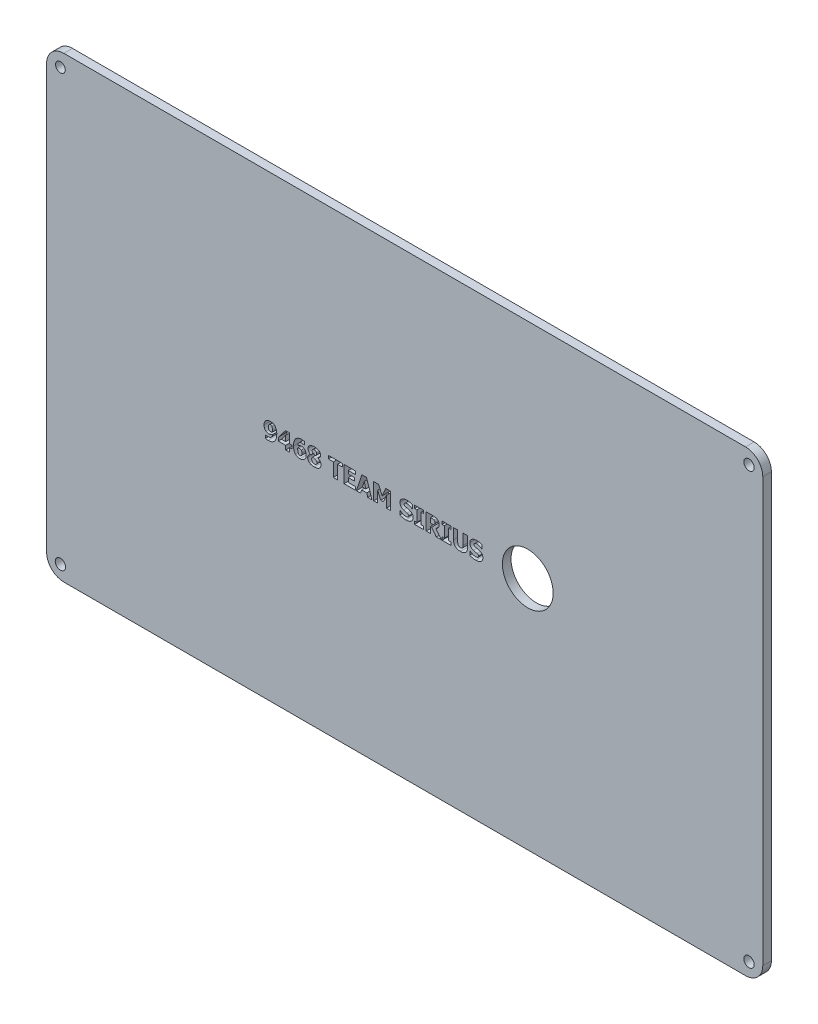
SolidWorks part; units mm, degrees
ref_plane "Ön Düzlem" through (0, 0, 0) normal (0, 0, 1) x (1, 0, 0)
ref_plane "Üst Düzlem" through (0, 0, 0) normal (0, 1, 0) x (1, 0, 0)
ref_plane "Sağ Düzlem" through (0, 0, 0) normal (1, 0, 0) x (0, 0, -1)
sketch "Çizim3" plane through (0, 0, 0) normal (0, 0, 1) x (1, 0, 0)
  line L0 (-198, 133) -> (198, 133)
  line L1 (-208, 123) -> (-208, -123)
  line L2 (-198, -133) -> (198, -133)
  line L3 (208, 123) -> (208, -123)
  arc A0 (208, 123) -> (198, 133) centre (198, 123) ccw
  arc A1 (198, -133) -> (208, -123) centre (198, -123) ccw
  arc A2 (-198, -133) -> (-208, -123) centre (-198, -123) cw
  arc A3 (-208, 123) -> (-198, 133) centre (-198, 123) cw
  circle A4 centre (71.4971, 3.5415) radius 14.751
  circle A5 centre (-200, 125) radius 2.8284
  circle A6 centre (-200, -125) radius 3
  circle A7 centre (200, -125) radius 3
  circle A8 centre (200, 125) radius 3
extrude "Yükseklik-Ekstrüzyon1" add sketch "Çizim3" along normal blind 5
sketch "Çizim4" plane through (0, 0, 5) normal (0, 0, 1) x (1, 0, 0)
  text T0 "<b>9468 TEAM SIRIUS</b>" font "Tahoma" height in points 36
extrude "Kes-Ekstrüzyon1" cut sketch "Çizim4" against normal blind 5
sketch "Çizim5" plane through (0, 0, 5) normal (0, 0, 1) x (1, 0, 0)
  line L0 (-208, 0) -> (208, 0) construction
  line L1 (-208, 123) -> (-208, -123) construction
  line L2 (208, -123) -> (208, 123) construction
  line L3 (-188, 133) -> (-188, -133) construction
  line L4 (198, 133) -> (-198, 133) construction
  line L5 (-198, -133) -> (198, -133) construction
  circle A0 centre (-188, 56.4) radius 1.5
  circle A1 centre (-188, -56.39) radius 1.5
  circle A2 centre (-124, 56.4) radius 1.5
  circle A3 centre (-124, -56.39) radius 1.5
  dimension "D2" = 112.79
  dimension "D4" = 64
  dimension "D1" = 20
  dimension "D3" = 56.4
  dimension "D5" = 64
sketch "Çizim6" plane through (0, 0, 5) normal (0, 0, 1) x (1, 0, 0)
  line L1 (-199.4772, 71.0652) -> (-109.5213, 71.0652)
  line L2 (-199.4772, 71.0652) -> (-199.4772, -69.7158)
  line L3 (-199.4772, -69.7158) -> (-109.5213, -69.7158)
  line L4 (-109.5213, 71.0652) -> (-109.5213, -69.7158)
